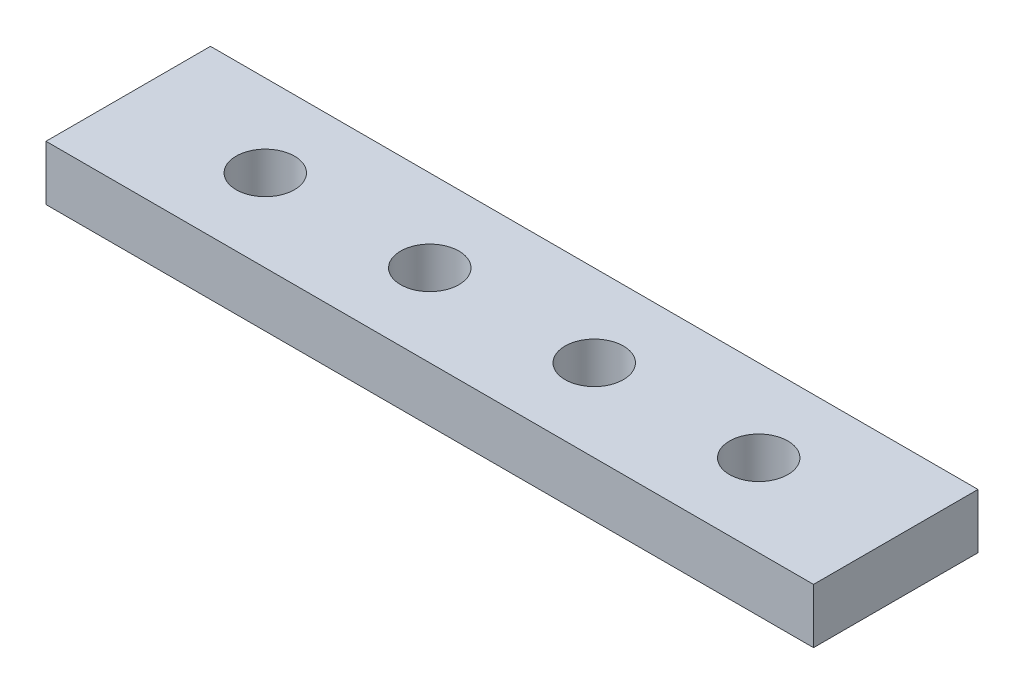
SolidWorks part; units mm, degrees
ref_plane "Front Plane" through (0, 0, 0) normal (0, 0, 1) x (1, 0, 0)
ref_plane "Top Plane" through (0, 0, 0) normal (0, 1, 0) x (1, 0, 0)
ref_plane "Right Plane" through (0, 0, 0) normal (1, 0, 0) x (0, 0, -1)
sketch "Sketch1" plane through (0, 0, 0) normal (0, 1, 0) x (1, 0, 0)
  line L1 (-44.45, -9.525) -> (44.45, -9.525)
  line L2 (-44.45, -9.525) -> (-44.45, 9.525)
  line L3 (-44.45, 9.525) -> (44.45, 9.525)
  line L4 (44.45, -9.525) -> (44.45, 9.525)
  line L5 (-44.45, -9.525) -> (44.45, 9.525) construction
  line L6 (-44.45, 9.525) -> (44.45, -9.525) construction
  point P0 (0, 0)
  dimension "D1" = 19.05
  dimension "D2" = 88.9
extrude "Boss-Extrude1" add sketch "Sketch1" along normal blind 6.35
hole_wizard "1/4 Clearance Hole1" positions "Sketch2" profile "Sketch3" hole size "1/4" standard "ANSI Inch" end condition through all
sketch "Sketch2" plane through (0, 0, 0) normal (0, -1, 0) x (-1, 0, 0)
  circle A8 centre (28.575, 0) radius 2.5527 construction
  circle A9 centre (9.525, 0) radius 2.5527 construction
  circle A10 centre (-9.525, 0) radius 2.5527 construction
  circle A11 centre (-28.575, 0) radius 2.5527 construction
  circle A12 centre (28.575, 0) radius 2.5527
  circle A13 centre (9.525, 0) radius 2.5527
  circle A14 centre (-9.525, 0) radius 2.5527
  circle A15 centre (-28.575, 0) radius 2.5527
  point P36 (28.575, 0)
  point P39 (9.525, 0)
  point P42 (-9.525, 0)
  point P45 (-28.575, 0)
sketch "Sketch3" plane through (28.575, 0, 0) normal (1, 0, 0) x (0, 0, -1)
  line L0 (0, 0) -> (0, 6.35)
  line L1 (0, 6.35) -> (3.3782, 6.35)
  line L2 (3.3782, 6.35) -> (3.3782, 0)
  line L5 (3.3782, 0) -> (0, 0)
  line L11 (0, -6.35) -> (0, 107.95) construction
  dimension "Thru Hole Dia." = 6.7564
  dimension "Thru Hole Depth" = 6.35
